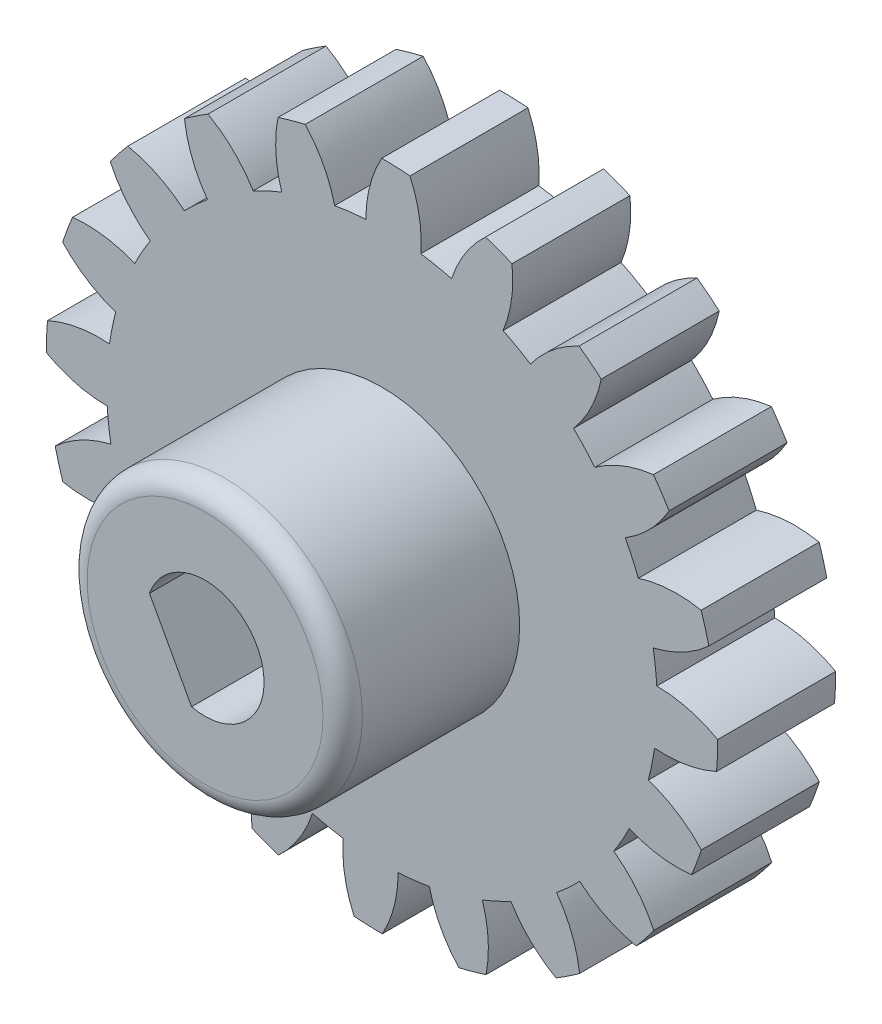
SolidWorks part; units mm, degrees
ref_plane "前视基准面" through (0, 0, 0) normal (0, 0, 1) x (1, 0, 0)
ref_plane "上视基准面" through (0, 0, 0) normal (0, 1, 0) x (1, 0, 0)
ref_plane "右视基准面" through (0, 0, 0) normal (1, 0, 0) x (0, 0, -1)
sketch "草图4" plane through (0, 0, 0) normal (0, 0, 1) x (1, 0, 0)
  arc A0 (6.9869, 0.4108) -> (6.8946, 1.2041) centre (0, 0) ccw
  arc A1 (8.7986, -0.1555) -> (6.9869, 0.4108) centre (6.981, -2.7892) ccw
  arc A2 (8.7815, -0.5703) -> (8.7986, -0.1555) centre (0, 0) ccw
  arc A3 (6.9293, -0.9854) -> (8.7815, -0.5703) centre (7.1871, 2.2042) ccw
  arc A4 (6.7719, -1.7684) -> (6.9293, -0.9854) centre (0, 0) ccw
  arc A5 (8.3199, -2.8668) -> (6.7719, -1.7684) centre (5.7774, -4.8099) ccw
  arc A6 (8.1755, -3.2561) -> (8.3199, -2.8668) centre (0, 0) ccw
  arc A7 (6.2856, -3.0784) -> (8.1755, -3.2561) centre (7.5165, -0.1246) ccw
  arc A8 (5.894, -3.7744) -> (6.2856, -3.0784) centre (0, 0) ccw
  arc A9 (7.0268, -5.2975) -> (5.894, -3.7744) centre (4.0083, -6.3598) ccw
  arc A10 (6.7691, -5.623) -> (7.0268, -5.2975) centre (0, 0) ccw
  arc A11 (5.0267, -4.8701) -> (6.7691, -5.623) centre (7.1101, -2.4413) ccw
  arc A12 (4.4392, -5.4111) -> (5.0267, -4.8701) centre (0, 0) ccw
  arc A13 (5.0459, -7.2096) -> (4.4392, -5.4111) centre (1.8468, -7.2872) ccw
  arc A14 (4.7002, -7.4396) -> (5.0459, -7.2096) centre (0, 0) ccw
  arc A15 (3.2757, -6.1851) -> (4.7002, -7.4396) centre (6.0077, -4.5189) ccw
  arc A16 (2.5498, -6.518) -> (3.2757, -6.1851) centre (0, 0) ccw
  arc A17 (2.571, -8.416) -> (2.5498, -6.518) centre (-0.4954, -7.5012) ccw
  arc A18 (2.1712, -8.5279) -> (2.571, -8.416) centre (0, 0) ccw
  arc A19 (1.2041, -6.8946) -> (2.1712, -8.5279) centre (4.3173, -6.1542) ccw
  arc A20 (0.4108, -6.9869) -> (1.2041, -6.8946) centre (0, 0) ccw
  arc A21 (-0.1555, -8.7986) -> (0.4108, -6.9869) centre (-2.7892, -6.981) ccw
  arc A22 (-0.5703, -8.7815) -> (-0.1555, -8.7986) centre (0, 0) ccw
  arc A23 (-0.9854, -6.9293) -> (-0.5703, -8.7815) centre (2.2042, -7.1871) ccw
  arc A24 (-1.7684, -6.7719) -> (-0.9854, -6.9293) centre (0, 0) ccw
  arc A25 (-2.8668, -8.3199) -> (-1.7684, -6.7719) centre (-4.8099, -5.7774) ccw
  arc A26 (-3.2561, -8.1755) -> (-2.8668, -8.3199) centre (0, 0) ccw
  arc A27 (-3.0784, -6.2856) -> (-3.2561, -8.1755) centre (-0.1246, -7.5165) ccw
  arc A28 (-3.7744, -5.894) -> (-3.0784, -6.2856) centre (0, 0) ccw
  arc A29 (-5.2975, -7.0268) -> (-3.7744, -5.894) centre (-6.3598, -4.0083) ccw
  arc A30 (-5.623, -6.7691) -> (-5.2975, -7.0268) centre (0, 0) ccw
  arc A31 (-4.8701, -5.0267) -> (-5.623, -6.7691) centre (-2.4413, -7.1101) ccw
  arc A32 (-5.4111, -4.4392) -> (-4.8701, -5.0267) centre (0, 0) ccw
  arc A33 (-7.2096, -5.0459) -> (-5.4111, -4.4392) centre (-7.2872, -1.8468) ccw
  arc A34 (-7.4396, -4.7002) -> (-7.2096, -5.0459) centre (0, 0) ccw
  arc A35 (-6.1851, -3.2757) -> (-7.4396, -4.7002) centre (-4.5189, -6.0077) ccw
  arc A36 (-6.518, -2.5498) -> (-6.1851, -3.2757) centre (0, 0) ccw
  arc A37 (-8.416, -2.571) -> (-6.518, -2.5498) centre (-7.5012, 0.4954) ccw
  arc A38 (-8.5279, -2.1712) -> (-8.416, -2.571) centre (0, 0) ccw
  arc A39 (-6.8946, -1.2041) -> (-8.5279, -2.1712) centre (-6.1542, -4.3173) ccw
  arc A40 (-6.9869, -0.4108) -> (-6.8946, -1.2041) centre (0, 0) ccw
  arc A41 (-8.7986, 0.1555) -> (-6.9869, -0.4108) centre (-6.981, 2.7892) ccw
  arc A42 (-8.7815, 0.5703) -> (-8.7986, 0.1555) centre (0, 0) ccw
  arc A43 (-6.9293, 0.9854) -> (-8.7815, 0.5703) centre (-7.1871, -2.2042) ccw
  arc A44 (-6.7719, 1.7684) -> (-6.9293, 0.9854) centre (0, 0) ccw
  arc A45 (-8.3199, 2.8668) -> (-6.7719, 1.7684) centre (-5.7774, 4.8099) ccw
  arc A46 (-8.1755, 3.2561) -> (-8.3199, 2.8668) centre (0, 0) ccw
  arc A47 (-6.2856, 3.0784) -> (-8.1755, 3.2561) centre (-7.5165, 0.1246) ccw
  arc A48 (-5.894, 3.7744) -> (-6.2856, 3.0784) centre (0, 0) ccw
  arc A49 (-7.0268, 5.2975) -> (-5.894, 3.7744) centre (-4.0083, 6.3598) ccw
  arc A50 (-6.7691, 5.623) -> (-7.0268, 5.2975) centre (0, 0) ccw
  arc A51 (-5.0267, 4.8701) -> (-6.7691, 5.623) centre (-7.1101, 2.4413) ccw
  arc A52 (-4.4392, 5.4111) -> (-5.0267, 4.8701) centre (0, 0) ccw
  arc A53 (-5.0459, 7.2096) -> (-4.4392, 5.4111) centre (-1.8468, 7.2872) ccw
  arc A54 (-4.7002, 7.4396) -> (-5.0459, 7.2096) centre (0, 0) ccw
  arc A55 (-3.2757, 6.1851) -> (-4.7002, 7.4396) centre (-6.0077, 4.5189) ccw
  arc A56 (-2.5498, 6.518) -> (-3.2757, 6.1851) centre (0, 0) ccw
  arc A57 (-2.571, 8.416) -> (-2.5498, 6.518) centre (0.4954, 7.5012) ccw
  arc A58 (-2.1712, 8.5279) -> (-2.571, 8.416) centre (0, 0) ccw
  arc A59 (-1.2041, 6.8946) -> (-2.1712, 8.5279) centre (-4.3173, 6.1542) ccw
  arc A60 (-0.4108, 6.9869) -> (-1.2041, 6.8946) centre (0, 0) ccw
  arc A61 (0.1555, 8.7986) -> (-0.4108, 6.9869) centre (2.7892, 6.981) ccw
  arc A62 (0.5703, 8.7815) -> (0.1555, 8.7986) centre (0, 0) ccw
  arc A63 (0.9854, 6.9293) -> (0.5703, 8.7815) centre (-2.2042, 7.1871) ccw
  arc A64 (1.7684, 6.7719) -> (0.9854, 6.9293) centre (0, 0) ccw
  arc A65 (2.8668, 8.3199) -> (1.7684, 6.7719) centre (4.8099, 5.7774) ccw
  arc A66 (3.2561, 8.1755) -> (2.8668, 8.3199) centre (0, 0) ccw
  arc A67 (3.0784, 6.2856) -> (3.2561, 8.1755) centre (0.1246, 7.5165) ccw
  arc A68 (3.7744, 5.894) -> (3.0784, 6.2856) centre (0, 0) ccw
  arc A69 (5.2975, 7.0268) -> (3.7744, 5.894) centre (6.3598, 4.0083) ccw
  arc A70 (5.623, 6.7691) -> (5.2975, 7.0268) centre (0, 0) ccw
  arc A71 (4.8701, 5.0267) -> (5.623, 6.7691) centre (2.4413, 7.1101) ccw
  arc A72 (5.4111, 4.4392) -> (4.8701, 5.0267) centre (0, 0) ccw
  arc A73 (7.2096, 5.0459) -> (5.4111, 4.4392) centre (7.2872, 1.8468) ccw
  arc A74 (7.4396, 4.7002) -> (7.2096, 5.0459) centre (0, 0) ccw
  arc A75 (6.1851, 3.2757) -> (7.4396, 4.7002) centre (4.5189, 6.0077) ccw
  arc A76 (6.518, 2.5498) -> (6.1851, 3.2757) centre (0, 0) ccw
  arc A77 (8.416, 2.571) -> (6.518, 2.5498) centre (7.5012, -0.4954) ccw
  arc A78 (8.5279, 2.1712) -> (8.416, 2.571) centre (0, 0) ccw
  arc A79 (6.8946, 1.2041) -> (8.5279, 2.1712) centre (6.1542, 4.3173) ccw
  circle A81 centre (0, 0) radius 8.5361
extrude "凸台-拉伸4" add sketch "草图4" along normal blind 3 contours A79 A81 A77 A76 A75 A73 A72 A71 A69 A68 A67 A65 A64 A63 A61 A60 A59 A57 A56 A55 A53 A52 A51 A49 A48 A47 A45 A44 A43 A41 A40 A39 A37 A36 A35 A33 A32 A31 A29
sketch "草图5" plane through (0, 0, 3) normal (0, 0, 1) x (1, 0, 0)
  circle A0 centre (0, 0) radius 3.5
extrude "凸台-拉伸6" add sketch "草图5" along normal blind 4.5
fillet "圆角1" radius 0.5 1 edges at (3.5, 0, 7.5)
sketch "草图8" plane through (0, 0, 0) normal (0, 0, -1) x (-1, 0, 0)
  line L0 (0.3425, -1.4604) -> (1.4133, 0.5026) construction
  line L1 (0.3425, -1.4604) -> (1.4133, 0.5026)
  arc A0 (1.4133, 0.5026) -> (0.3425, -1.4604) centre (0, 0) ccw construction
  arc A1 (1.4133, 0.5026) -> (0.3425, -1.4604) centre (0, 0) ccw
extrude "切除-拉伸1" cut sketch "草图8" against normal through all
